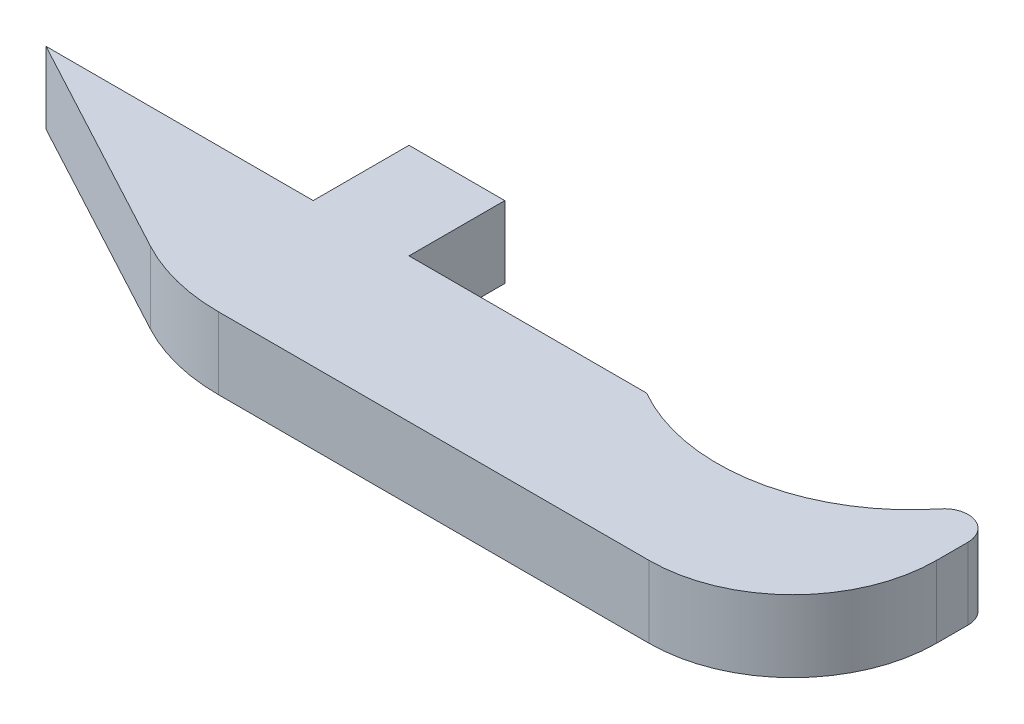
SolidWorks part; units mm, degrees
material "AISI 4130 Steel, annealed at 865C"
ref_plane "X-Y Datum" through (0, 0, 0) normal (0, 0, 1) x (1, 0, 0)
ref_plane "X-Z Datum" through (0, 0, 0) normal (0, 1, 0) x (1, 0, 0)
ref_plane "Y-Z Datum" through (0, 0, 0) normal (1, 0, 0) x (0, 0, -1)
sketch "Sketch1" plane through (0, 0, 0) normal (0, 1, 0) x (1, 0, 0)
  line L0 (20.8895, 0) -> (0, 0) construction
  line L1 (49.3776, 0) -> (0, 0)
  line L2 (49.3776, 0) -> (49.3776, 11.1252)
  line L3 (20.9296, -9.525) -> (62.2046, -9.525)
  line L4 (62.2046, 11.1252) -> (62.2046, -9.525)
  line L5 (3.175, 0) -> (20.9296, -9.525)
  circle A0 centre (49.3776, 11.1252) radius 12.827
  dimension "D3" = 25.654
  dimension "D5" = 9.525
  dimension "D1" = 49.3776
  dimension "D2" = 11.1252
  dimension "D4" = 3.175
  dimension "D6" = 41.275
extrude "Boss-Extrude1" add sketch "Sketch1" along normal blind 4.7625
fillet "Fillet1" radius 9.525 1 edges at (62.2046, 2.3813, 9.525)
fillet "Fillet2" radius 1.5875 1 edges at (62.2046, 2.3813, -11.1252)
fillet "Fillet4" radius 12.7 1 edges at (20.9296, 2.3813, 9.525)
sketch "Sketch2" plane through (0, 0, 0) normal (0, -1, 0) x (1, 0, 0)
  line L1 (27.2395, -6.35) -> (27.2395, 0)
  line L2 (-7.0505, -6.35) -> (27.8745, -6.35) construction
  line L3 (27.2395, 0) -> (20.8895, 0)
  line L4 (27.2395, 0) -> (27.2395, -6.35)
  line L5 (27.2395, -6.35) -> (20.8895, -6.35)
  line L6 (20.8895, 0) -> (20.8895, -6.35)
  line L7 (33.5895, 0) -> (33.5895, -6.35) construction
  line M6 (3.175, 0) -> (42.9931, 0)
  dimension "D1" = 6.35
  dimension "D2" = 6.35
extrude "Boss-Extrude2" add sketch "Sketch2" against normal blind 4.7625 contours L6 L5 L1 M6
